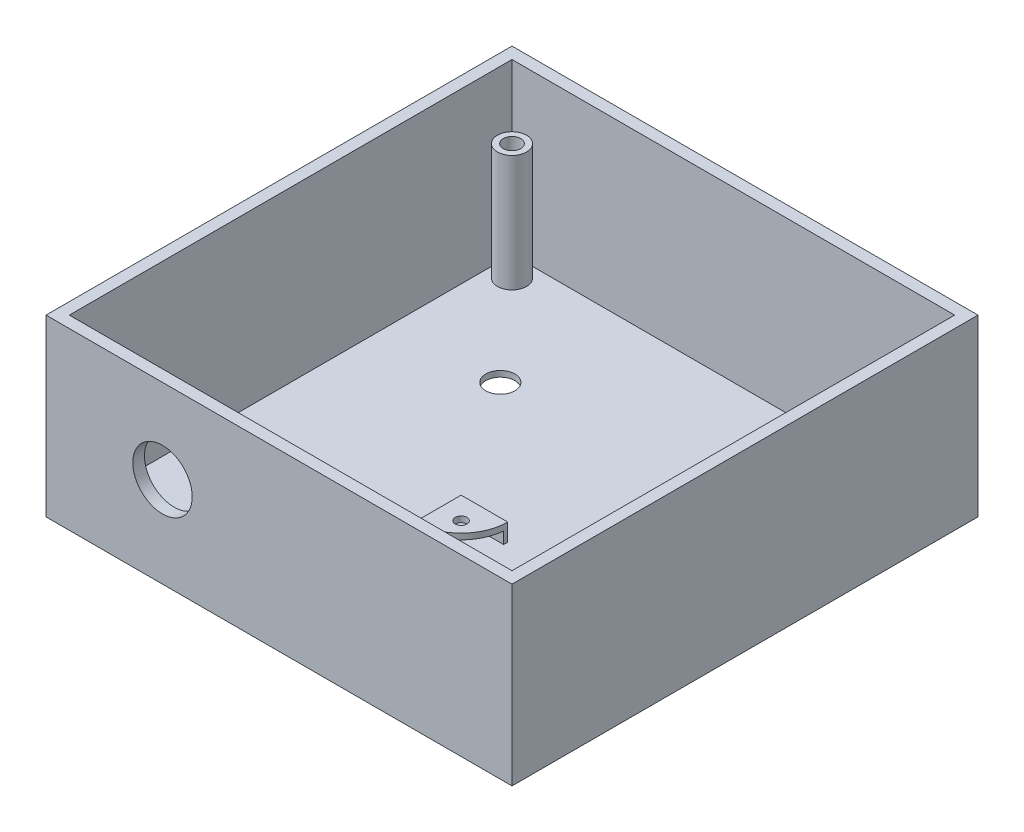
SolidWorks part; units mm, degrees
ref_plane "Front Plane" through (0, 0, 0) normal (0, 0, 1) x (1, 0, 0)
ref_plane "Top Plane" through (0, 0, 0) normal (0, 1, 0) x (1, 0, 0)
ref_plane "Right Plane" through (0, 0, 0) normal (1, 0, 0) x (0, 0, -1)
sketch "Sketch1" plane through (0, 0, 0) normal (0, 1, 0) x (1, 0, 0)
  line L1 (-40, 40) -> (40, 40)
  line L2 (-40, 40) -> (-40, -40)
  line L3 (-40, -40) -> (40, -40)
  line L4 (40, 40) -> (40, -40)
  line L5 (-40, 40) -> (40, -40) construction
  line L6 (-40, -40) -> (40, 40) construction
  point P0 (0, 0)
  dimension "D1" = 80
  dimension "D2" = 80
extrude "Boss-Extrude1" add sketch "Sketch1" along normal blind 30
sketch "Sketch2" plane through (0, 30, 0) normal (0, 1, 0) x (1, 0, 0)
  line L1 (-38, 38) -> (38, 38)
  line L2 (-38, 38) -> (-38, -38)
  line L3 (-38, -38) -> (38, -38)
  line L4 (38, 38) -> (38, -38)
  line L5 (-38, 38) -> (38, -38) construction
  line L6 (-38, -38) -> (38, 38) construction
  point P0 (0, 0)
  dimension "D1" = 76
  dimension "D2" = 76
extrude "Cut-Extrude1" cut sketch "Sketch2" against normal blind 29
sketch "Sketch3" plane through (0, 1, 0) normal (0, 1, 0) x (1, 0, 0)
  line L0 (-38, 38) -> (-38, -38) construction
  line L1 (38, 38) -> (-38, 38) construction
  line L2 (38, -38) -> (38, 38) construction
  line L3 (38, 38) -> (-38, 38) construction
  line L4 (-38, 38) -> (-38, -38) construction
  line L5 (-38, -38) -> (38, -38) construction
  circle A0 centre (-34.5, 34.5) radius 2.5
  circle A1 centre (-34.5, 34.5) radius 1.5
  circle A2 centre (34.5, 34.5) radius 2.5
  circle A3 centre (34.5, 34.5) radius 1.5
  circle A4 centre (-34.5, -34.5) radius 2.5
  circle A5 centre (-34.5, -34.5) radius 1.5
  circle A6 centre (34.5, -34.5) radius 2.5
  circle A7 centre (34.5, -34.5) radius 1.5
  dimension "D1" = 3.5
  dimension "D3" = 3.5
  dimension "D5" = 3.5
  dimension "D2" = 3.5
  dimension "D4" = 3.5
  dimension "D6" = 3.5
extrude "Boss-Extrude5" add sketch "Sketch3" along normal blind 20
sketch "Sketch4" plane through (0, 0, 0) normal (0, -1, 0) x (1, 0, 0)
  circle A0 centre (-20, -18) radius 2.5
extrude "Cut-Extrude2" cut sketch "Sketch4" against normal blind 10
sketch "Sketch5" plane through (0, 0, 0) normal (0, -1, 0) x (1, 0, 0)
  line L0 (40, 40) -> (40, -40) construction
  line L1 (-1.5, 30.6914) -> (25, 30.6914)
  line L2 (-1.5, 30.6914) -> (-1.5, 15.1914)
  line L3 (-1.5, 15.1914) -> (25, 15.1914)
  line L4 (25, 30.6914) -> (25, 15.1914)
  line L6 (25.1, 34.9914) -> (-1.6, 34.9914) construction
  dimension "D1" = 26.5
  dimension "D2" = 15.5
  dimension "D3" = 15
  dimension "D5" = 4.3
extrude "Cut-Extrude3" cut sketch "Sketch5" against normal blind 25
sketch "Sketch6" plane through (0, 0, 40) normal (0, 0, 1) x (1, 0, 0)
  circle A0 centre (-20, 15.5368) radius 5.1
extrude "Cut-Extrude4" cut sketch "Sketch6" against normal blind 10
sketch "Sketch7" plane through (0, 1, 0) normal (0, 1, 0) x (1, 0, 0)
  line L0 (25, -30.6914) -> (25, -15.1914) construction
  line L1 (-1.6, -7.1314) -> (25.1, -7.1314)
  line L2 (-1.6, -7.1314) -> (-1.6, -34.9914)
  line L3 (-1.6, -34.9914) -> (25.1, -34.9914)
  line L4 (25.1, -7.1314) -> (25.1, -34.9914)
  line L5 (-1.5, -15.1914) -> (-1.5, -30.6914) construction
  line L7 (25.1, -34.9914) -> (-1.6, -34.9914) construction
  line L8 (23.3, -7.1314) -> (18.2531, -7.1314) construction
  dimension "D1" = 0.1
  dimension "D2" = 0.1
  dimension "D4" = 0
  dimension "D5" = 26.7
  dimension "D6" = 0
sketch "Sketch9" plane through (0, 1, 0) normal (0, 1, 0) x (1, 0, 0)
  line L0 (-1.6, -7.1314) -> (-1.6, -34.9914) construction
  line L1 (-1.6, -7.1314) -> (25.1, -7.1314) construction
  line L2 (25.1, -7.1314) -> (25.1, -34.9914) construction
  line L3 (-1.6, -34.9914) -> (25.1, -34.9914) construction
  circle A0 centre (0.2, -8.9314) radius 1.8
  circle A1 centre (23.3, -8.9314) radius 1.8
  circle A2 centre (0.2, -33.1914) radius 1.8
  circle A3 centre (23.3, -33.1914) radius 1.8
  dimension "D1" = 1.8
  dimension "D3" = 1.8
  dimension "D4" = 1.8
  dimension "D2" = 1.8
sketch "Sketch10" plane through (0, 1, 0) normal (0, 1, 0) x (1, 0, 0)
  circle A0 centre (0.2, -8.9314) radius 1
  circle A1 centre (23.3, -8.9314) radius 1
  circle A2 centre (0.2, -33.1914) radius 1
  circle A3 centre (23.3, -33.1914) radius 1
sketch "Sketch11" plane through (0, 1, 0) normal (0, 1, 0) x (1, 0, 0)
  line L0 (-3.6, -5.1314) -> (-3.6, -13.1314)
  line L1 (-3.6, -5.1314) -> (4.4, -5.1314)
  line L2 (19.1, -5.1314) -> (27.1, -5.1314)
  line L3 (27.1, -5.1314) -> (27.1, -13.1314)
  line L4 (27.1, -28.4914) -> (27.1, -36.4914)
  line L5 (27.1, -36.4914) -> (19.1, -36.4914)
  line L6 (4.4, -36.4914) -> (-3.6, -36.4914)
  line L7 (-3.6, -36.4914) -> (-3.6, -28.4914)
  line L8 (-1.6, -7.1314) -> (-1.6, -34.9914) construction
  line L9 (-1.6, -7.1314) -> (25.1, -7.1314) construction
  line L10 (25.1, -7.1314) -> (25.1, -34.9914) construction
  line L11 (-1.6, -34.9914) -> (25.1, -34.9914) construction
  arc A0 (4.4, -5.1314) -> (-3.6, -13.1314) centre (-3.6, -5.1314) cw
  arc A1 (27.1, -13.1314) -> (19.1, -5.1314) centre (27.1, -5.1314) cw
  arc A2 (27.1, -28.4914) -> (19.1, -36.4914) centre (27.1, -36.4914) ccw
  arc A3 (-3.6, -28.4914) -> (4.4, -36.4914) centre (-3.6, -36.4914) cw
  dimension "D1" = 2
  dimension "D2" = 2
  dimension "D3" = 2
  dimension "D4" = 2
  dimension "D5" = 2
  dimension "D6" = 1.5
  dimension "D7" = 1.5
  dimension "D8" = 2
sketch "Sketch12" plane through (0, 1, 0) normal (0, 1, 0) x (1, 0, 0)
  line L0 (-2.9, -13.1007) -> (-2.9, -5.8314)
  line L1 (-2.9, -5.8314) -> (4.3693, -5.8314)
  line L2 (19.1307, -5.8314) -> (26.4, -5.8314)
  line L3 (26.4, -5.8314) -> (26.4, -13.1007)
  line L4 (26.4, -35.4914) -> (26.4, -28.5221)
  line L5 (26.4, -35.4914) -> (19.4307, -35.4914)
  line L6 (4.3373, -35.4914) -> (-2.9, -35.4914)
  line L7 (-2.9, -35.4914) -> (-2.9, -28.2542)
  line L8 (-1.6, -7.1314) -> (-1.6, -34.9914) construction
  line L9 (-1.6, -7.1314) -> (25.1, -7.1314) construction
  line L10 (25.1, -7.1314) -> (25.1, -34.9914) construction
  line L11 (-1.6, -34.9914) -> (25.1, -34.9914) construction
  arc A0 (4.3693, -5.8314) -> (-2.9, -13.1007) centre (-2.9, -5.8314) cw
  arc A1 (-3.6, -13.1314) -> (4.4, -5.1314) centre (-3.6, -5.1314) ccw construction
  arc A2 (26.4, -13.1007) -> (19.1307, -5.8314) centre (26.4, -5.8314) cw
  arc A3 (19.1, -5.1314) -> (27.1, -13.1314) centre (27.1, -5.1314) ccw construction
  arc A4 (26.4, -28.5221) -> (19.4307, -35.4914) centre (26.4, -35.4914) ccw
  arc A5 (27.1, -28.4914) -> (19.1, -36.4914) centre (27.1, -36.4914) ccw construction
  arc A6 (4.3373, -35.4914) -> (-2.9, -28.2542) centre (-2.9, -35.4914) ccw
  arc A7 (4.4, -36.4914) -> (-3.6, -28.4914) centre (-3.6, -36.4914) ccw construction
  dimension "D1" = 1.3
  dimension "D2" = 1.3
  dimension "D3" = 1.3
  dimension "D4" = 1.3
  dimension "D5" = 1.3
  dimension "D6" = 0.5
  dimension "D7" = 0.5
  dimension "D8" = 1.3
extrude "Boss-Extrude6" add sketch "Sketch11" along normal blind 3
extrude "Cut-Extrude5" cut sketch "Sketch12" along normal blind 2
extrude "Cut-Extrude6" cut sketch "Sketch10" along normal blind 3
